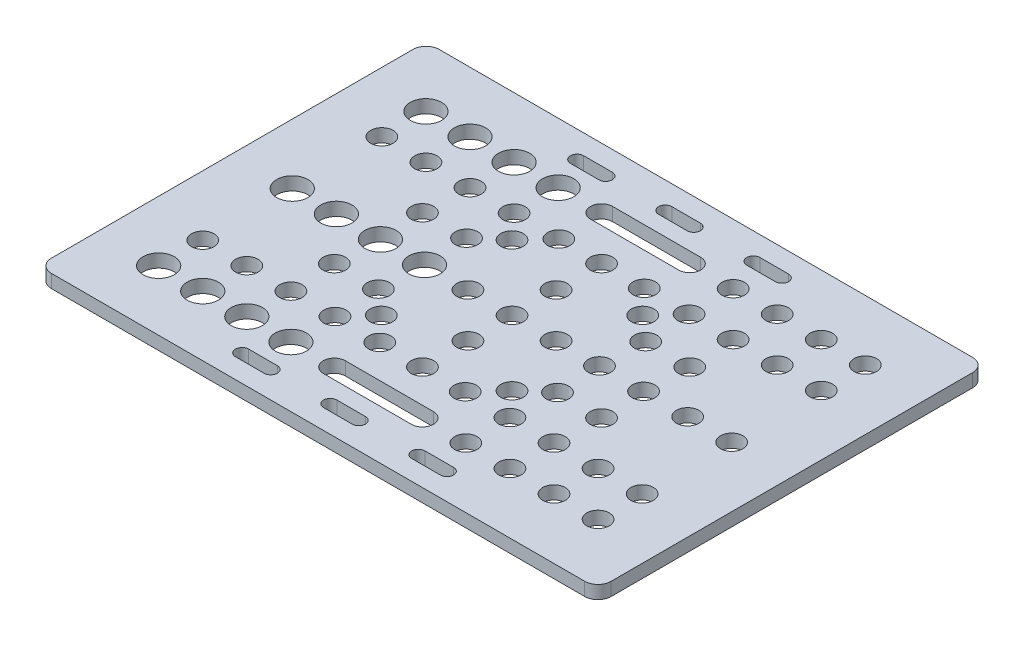
SolidWorks part; units mm, degrees
material "6061-T6 (SS)"
ref_plane "Front Plane" through (0, 0, 0) normal (0, 0, 1) x (1, 0, 0)
ref_plane "Top Plane" through (0, 0, 0) normal (0, 1, 0) x (1, 0, 0)
ref_plane "Right Plane" through (0, 0, 0) normal (1, 0, 0) x (0, 0, -1)
sketch "Sketch1" plane through (0, 0, 0) normal (0, 1, 0) x (1, 0, 0)
  line L0 (0, 0) -> (63.5, 0) construction
  line L1 (60.5, -44) -> (-60.5, -44)
  line L2 (63.5, -41) -> (63.5, 41)
  line L3 (60.5, 44) -> (-60.5, 44)
  line L4 (-63.5, -41) -> (-63.5, 41)
  line L5 (0, 44) -> (0, 0) construction
  line L6 (-49.85, 30.32) -> (-39.85, 30.32) construction
  line L7 (49.85, 30.32) -> (39.85, 30.32) construction
  line L8 (49.85, 0) -> (39.85, 0) construction
  line L9 (10, 30.32) -> (-10, 30.32) construction
  line L10 (10, 27.82) -> (-10, 27.82)
  line L11 (10, 32.82) -> (-10, 32.82)
  line L12 (3.25, 38) -> (-3.25, 38) construction
  line L13 (3.25, 36.5) -> (-3.25, 36.5)
  line L14 (3.25, 39.5) -> (-3.25, 39.5)
  line L15 (-16.75, 38) -> (-23.25, 38) construction
  line L16 (-16.75, 36.5) -> (-23.25, 36.5)
  line L17 (-16.75, 39.5) -> (-23.25, 39.5)
  line L18 (16.75, 38) -> (23.25, 38) construction
  line L19 (16.75, 36.5) -> (23.25, 36.5)
  line L20 (16.75, 39.5) -> (23.25, 39.5)
  line L21 (10, -30.32) -> (-10, -30.32) construction
  line L22 (10, -27.82) -> (-10, -27.82)
  line L23 (10, -32.82) -> (-10, -32.82)
  line L24 (-16.75, -38) -> (-23.25, -38) construction
  line L25 (-16.75, -36.5) -> (-23.25, -36.5)
  line L26 (-16.75, -39.5) -> (-23.25, -39.5)
  line L27 (3.25, -38) -> (-3.25, -38) construction
  line L28 (3.25, -36.5) -> (-3.25, -36.5)
  line L29 (3.25, -39.5) -> (-3.25, -39.5)
  line L30 (16.75, -38) -> (23.25, -38) construction
  line L31 (16.75, -36.5) -> (23.25, -36.5)
  line L32 (16.75, -39.5) -> (23.25, -39.5)
  arc A0 (-60.5, -44) -> (-63.5, -41) centre (-60.5, -41) cw
  arc A1 (60.5, -44) -> (63.5, -41) centre (60.5, -41) ccw
  arc A2 (63.5, 41) -> (60.5, 44) centre (60.5, 41) ccw
  arc A3 (-60.5, 44) -> (-63.5, 41) centre (-60.5, 41) ccw
  circle A4 centre (-39.85, 30.32) radius 3.55
  circle A5 centre (0, 10) radius 2.55
  circle A6 centre (0, 0) radius 2.55
  circle A7 centre (10, 0) radius 2.55
  circle A8 centre (-10, 0) radius 2.55
  circle A9 centre (-49.85, 30.32) radius 3.55
  circle A10 centre (-49.85, 0) radius 3.55
  circle A11 centre (-49.85, -30.32) radius 3.55
  circle A12 centre (-20.32, 10) radius 2.55
  circle A13 centre (-30.32, 10) radius 2.55
  circle A14 centre (-14.825, 14.825) radius 2.55
  circle A15 centre (0, 20.32) radius 2.55
  circle A16 centre (-49.85, 20.32) radius 2.55
  circle A17 centre (-39.85, 20.32) radius 2.55
  circle A18 centre (-29.85, 20.32) radius 2.55
  circle A19 centre (-39.85, 0) radius 3.55
  circle A20 centre (14.825, 14.825) radius 2.55
  circle A21 centre (20.32, 10) radius 2.55
  circle A22 centre (30.32, 10) radius 2.55
  circle A23 centre (39.85, 30.32) radius 2.55
  circle A24 centre (49.85, 30.32) radius 2.55
  circle A25 centre (49.85, 0) radius 2.55
  circle A26 centre (30.32, -10) radius 2.55
  circle A27 centre (49.85, -30.32) radius 2.55
  circle A28 centre (29.85, 30.32) radius 2.55
  circle A29 centre (20.32, -10) radius 2.55
  circle A30 centre (0, -10) radius 2.55
  circle A31 centre (14.825, -14.825) radius 2.55
  circle A32 centre (-29.85, 0) radius 3.55
  circle A33 centre (-19.85, 20.32) radius 2.55
  circle A34 centre (-9.69, 20.32) radius 2.55
  circle A35 centre (9.69, 20.32) radius 2.55
  circle A36 centre (-19.85, 0) radius 3.55
  circle A37 centre (-14.825, -14.825) radius 2.55
  circle A38 centre (-20.32, -10) radius 2.55
  circle A39 centre (-30.32, -10) radius 2.55
  circle A40 centre (-29.85, 30.32) radius 3.55
  circle A41 centre (-19.85, 30.32) radius 3.55
  circle A42 centre (19.85, 30.32) radius 2.55
  circle A43 centre (19.85, 20.32) radius 2.55
  circle A44 centre (29.85, 20.32) radius 2.55
  circle A45 centre (39.85, 20.32) radius 2.55
  circle A46 centre (49.85, 20.32) radius 2.55
  circle A47 centre (39.85, 0) radius 2.55
  circle A48 centre (29.85, 0) radius 2.55
  circle A49 centre (19.85, 0) radius 2.55
  circle A50 centre (19.85, -30.32) radius 2.55
  circle A51 centre (29.85, -30.32) radius 2.55
  circle A52 centre (0, -20.32) radius 2.55
  circle A53 centre (39.85, -30.32) radius 2.55
  circle A54 centre (49.85, -20.32) radius 2.55
  circle A55 centre (39.85, -20.32) radius 2.55
  circle A56 centre (29.85, -20.32) radius 2.55
  circle A57 centre (19.85, -20.32) radius 2.55
  circle A58 centre (9.69, -20.32) radius 2.55
  circle A59 centre (-9.69, -20.32) radius 2.55
  circle A60 centre (-19.85, -20.32) radius 2.55
  circle A61 centre (-29.85, -20.32) radius 2.55
  circle A62 centre (-39.85, -20.32) radius 2.55
  circle A63 centre (-49.85, -20.32) radius 2.55
  circle A64 centre (-19.85, -30.32) radius 3.55
  circle A65 centre (-29.85, -30.32) radius 3.55
  circle A66 centre (-39.85, -30.32) radius 3.55
  arc A67 (10, 27.82) -> (10, 32.82) centre (10, 30.32) ccw
  arc A68 (-10, 32.82) -> (-10, 27.82) centre (-10, 30.32) ccw
  arc A69 (3.25, 36.5) -> (3.25, 39.5) centre (3.25, 38) ccw
  arc A70 (-3.25, 39.5) -> (-3.25, 36.5) centre (-3.25, 38) ccw
  arc A71 (-16.75, 36.5) -> (-16.75, 39.5) centre (-16.75, 38) ccw
  arc A72 (-23.25, 39.5) -> (-23.25, 36.5) centre (-23.25, 38) ccw
  arc A73 (16.75, 36.5) -> (16.75, 39.5) centre (16.75, 38) cw
  arc A74 (23.25, 39.5) -> (23.25, 36.5) centre (23.25, 38) cw
  arc A75 (10, -27.82) -> (10, -32.82) centre (10, -30.32) cw
  arc A76 (-10, -32.82) -> (-10, -27.82) centre (-10, -30.32) cw
  arc A77 (-16.75, -36.5) -> (-16.75, -39.5) centre (-16.75, -38) cw
  arc A78 (-23.25, -39.5) -> (-23.25, -36.5) centre (-23.25, -38) cw
  arc A79 (3.25, -36.5) -> (3.25, -39.5) centre (3.25, -38) cw
  arc A80 (-3.25, -39.5) -> (-3.25, -36.5) centre (-3.25, -38) cw
  arc A81 (16.75, -36.5) -> (16.75, -39.5) centre (16.75, -38) ccw
  arc A82 (23.25, -39.5) -> (23.25, -36.5) centre (23.25, -38) ccw
  circle A86 centre (39.85, 0) radius 2.55 [skipped]
  point P0 (0, 0)
  point P149 (0, 30.32)
  point P156 (0, 38)
  point P162 (-20, 38)
  point P170 (20, 38)
  point P177 (0, -30.32)
  point P184 (-20, -38)
  point P191 (0, -38)
  point P198 (20, -38)
  dimension "D2" = 3
  dimension "D3" = 5.1
  dimension "D5" = 7.1
  dimension "D7" = 4
  dimension "D10" = 10
  dimension "D19" = 10
  dimension "D32" = 5.1
  dimension "D1" = 88
  dimension "D4" = 10
  dimension "D6" = 60.64
  dimension "D8" = 13.65
  dimension "D9" = 127
  dimension "D11" = 10
  dimension "D12" = 4
  dimension "D13" = 10
  dimension "D14" = 10
  dimension "D15" = 20.32
  dimension "D16" = 99.7
  dimension "D17" = 4
  dimension "D18" = 10
  dimension "D20" = 29.65
  dimension "D21" = 29.65
  dimension "D22" = 10.16
  dimension "D24" = 10
  dimension "D25" = 5
  dimension "D26" = 20
  dimension "D27" = 6.5
  dimension "D28" = 3
  dimension "D29" = 20
  dimension "D30" = 60.64
  dimension "D31" = 76
  dimension "D23" = 4
extrude "Boss-Extrude1" add sketch "Sketch1" along normal blind 3
